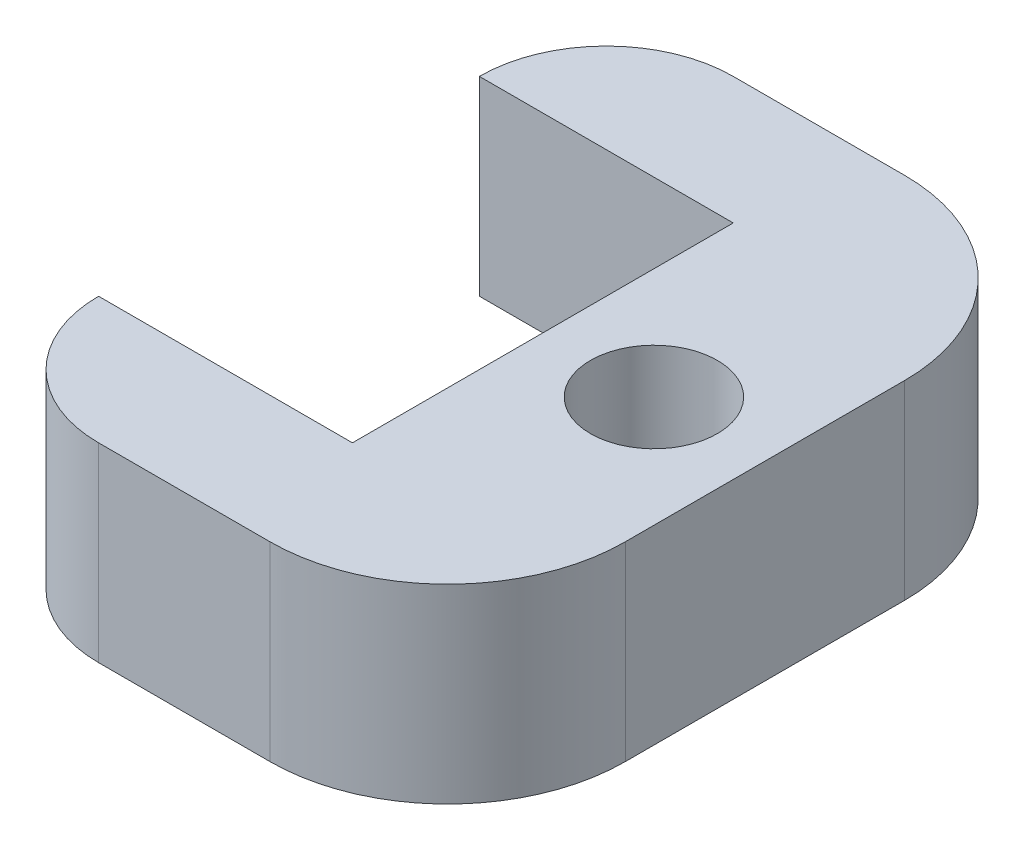
SolidWorks part; units mm, degrees
ref_plane "Front Plane" through (0, 0, 0) normal (0, 0, 1) x (1, 0, 0)
ref_plane "Top Plane" through (0, 0, 0) normal (0, 1, 0) x (1, 0, 0)
ref_plane "Right Plane" through (0, 0, 0) normal (1, 0, 0) x (0, 0, -1)
sketch "Sketch2" plane through (0, 0, 0) normal (0, 1, 0) x (1, 0, 0)
  line L0 (0, -38.1) -> (0, 38.1)
  line L1 (0, 38.1) -> (-50.8, 38.1)
  line L2 (-25.4, 63.5) -> (8.89, 63.5)
  line L3 (44.45, 27.94) -> (44.45, -27.94)
  line L4 (0, 0) -> (44.45, 0) construction
  line L5 (-25.4, -63.5) -> (8.89, -63.5)
  line L6 (0, -38.1) -> (-50.8, -38.1)
  arc A0 (-50.8, 38.1) -> (-25.4, 63.5) centre (-25.4, 38.1) cw
  arc A1 (-50.8, -38.1) -> (-25.4, -63.5) centre (-25.4, -38.1) ccw
  circle A2 centre (22.225, 0) radius 12.7
  arc A3 (8.89, -63.5) -> (44.45, -27.94) centre (8.89, -27.94) ccw
  arc A4 (8.89, 63.5) -> (44.45, 27.94) centre (8.89, 27.94) cw
  point P8 (44.45, 0)
  point P14 (44.45, 0)
  point P17 (22.225, 0)
  point P20 (44.45, -63.5)
  point P23 (44.45, 63.5)
  dimension "D5" = 25.4
  dimension "D6" = 35.56
  dimension "D1" = 127
  dimension "D2" = 50.8
  dimension "D3" = 95.25
  dimension "D4" = 25.4
extrude "Boss-Extrude1" add sketch "Sketch2" along normal blind 38.1
